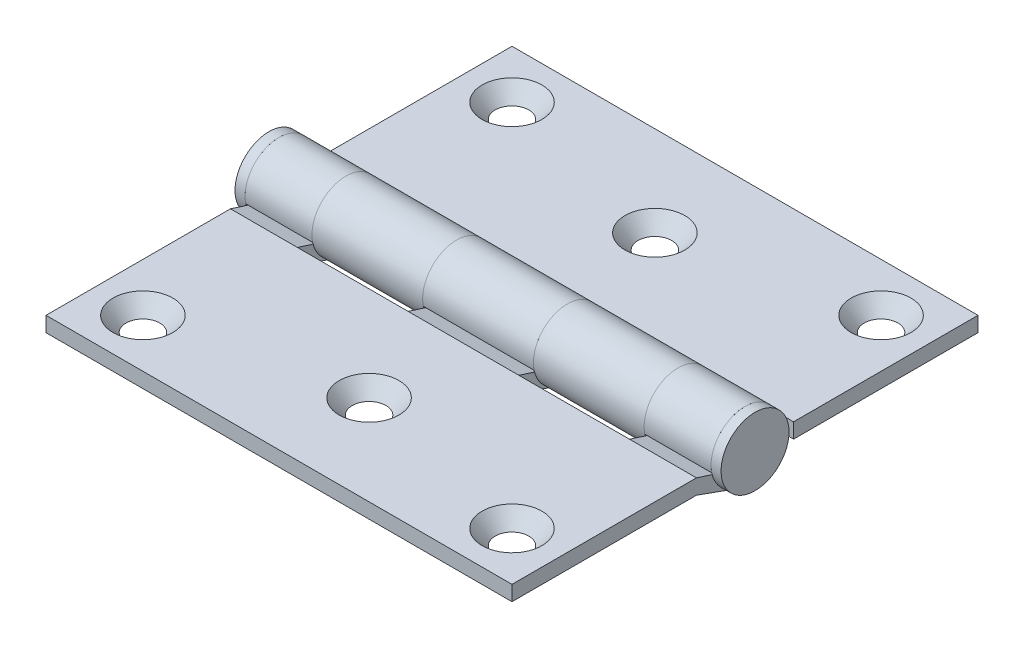
SolidWorks part; units mm, degrees
ref_plane "Front" through (0, 0, 0) normal (0, 0, 1) x (1, 0, 0)
ref_plane "Top" through (0, 0, 0) normal (0, 1, 0) x (1, 0, 0)
ref_plane "Right" through (0, 0, 0) normal (1, 0, 0) x (0, 0, -1)
sketch "Sketch1" plane through (0, 0, 0) normal (1, 0, 0) x (0, 0, -1)
  line L0 (-7.9375, -3.048) -> (-1.8819, -5.2279)
  line L1 (-38.1, -0.5842) -> (-7.9375, -0.5842)
  line L2 (-7.9375, -0.5842) -> (-0.9076, -2.8348)
  line L3 (-38.1, -3.048) -> (-7.9375, -3.048)
  line L4 (-38.1, -0.5842) -> (-38.1, -3.048)
  line L5 (-5.443, -1.1161) -> (-1.976, -2.2261)
  arc A0 (-0.9076, -2.8348) -> (-1.976, -2.2261) centre (0, 0) ccw
  arc A1 (-1.8819, -5.2279) -> (-5.443, -1.1161) centre (0, 0) ccw
  circle A2 centre (0, 0) radius 5.5562 construction
  circle A3 centre (0, 0) radius 2.9766 construction
  dimension "Pin Dia." = 5.9531
  dimension "Kn Dia" = 11.1125
  dimension "Th" = 2.4638
  dimension "D3" = 0.254
  dimension "Open Width / 2" = 38.1
  dimension "Leaf End" = 30.1625
  dimension "Leaf Top" = 0.5842
extrude "Left Leaf" add sketch "Sketch1" along normal mid plane 76.2
sketch "Sketch2" plane through (0, 0, 0) normal (0, 1, 0) x (1, 0, 0)
  line L0 (27.1577, -7.9375) -> (27.1577, 5.5563)
  line L2 (0, 5.5562) -> (0, -38.1) construction
  line L3 (38.1, 5.5563) -> (-38.1, 5.5563) construction
  line L4 (27.1577, 5.5563) -> (9.0526, 5.5563)
  line L5 (9.0526, 5.5563) -> (9.0526, -7.9375)
  line L7 (38.1, -38.1) -> (-38.1, -38.1) construction
  line L8 (-27.1577, -7.9375) -> (-27.1577, 5.5562)
  line L9 (9.0526, -7.9375) -> (27.1577, -7.9375)
  line L10 (-9.0526, -7.9375) -> (-27.1577, -7.9375)
  line L11 (-9.0526, 5.5563) -> (-9.0526, -7.9375)
  line L12 (-27.1577, 5.5562) -> (-9.0526, 5.5563)
  line L14 (-9.0526, 5.5563) -> (9.0526, 5.5563) construction
  dimension "Knuckle Lg" = 18.1051
extrude "Cut-Extrude1" cut sketch "Sketch2" against normal through all and the other way through all
sketch "Sketch3" plane through (27.1577, 0, 0) normal (1, 0, 0) x (0, 0, -1)
  line L0 (0, 5.5563) -> (0, -3.048) construction
  line L1 (-38.1, -3.048) -> (-7.9375, -3.048) construction
  line L2 (7.9375, -3.048) -> (1.8819, -5.2279)
  line L3 (7.9375, -0.5842) -> (0.9076, -2.8348)
  line L4 (1.976, -2.2261) -> (5.443, -1.1161)
  line L6 (7.9375, -3.048) -> (38.1, -3.048)
  line L7 (38.1, -3.048) -> (38.1, -0.5842)
  line L9 (-38.1, -0.5842) -> (-38.1, -3.048) construction
  line L10 (38.1, -0.5842) -> (7.9375, -0.5842)
  arc A0 (-1.8819, -5.2279) -> (-5.443, -1.1161) centre (0, 0) ccw construction
  circle A5 centre (0, 0) radius 5.5563 construction
  arc A6 (1.8819, -5.2279) -> (5.443, -1.1161) centre (0, 0) cw
  arc A7 (-0.9076, -2.8348) -> (-1.976, -2.2261) centre (0, 0) ccw construction
  arc A8 (1.976, -2.2261) -> (0.9076, -2.8348) centre (0, 0) ccw
extrude "Right Leaf" add sketch "Sketch3" against normal up to surface (18.1051 mm away) separate body up to face at (9.0526, -0.5185, 2.5509)
mirror "Mirror1" about plane through (0, 0, 0) normal (1, 0, 0) of bodies 110
sketch "Sketch4" plane through (0, 0, 0) normal (-1, 0, 0) x (0, 0, 1)
  line L0 (-7.9375, -0.5842) -> (-7.9375, -3.048)
  line L1 (-38.1, -0.5842) -> (-7.9375, -0.5842)
  line L2 (0, 5.5563) -> (0, -3.048) construction
  line L6 (-7.9375, -3.048) -> (-38.1, -3.048)
  line L8 (-38.1, -3.048) -> (-38.1, -0.5842)
extrude "Extrude3" add sketch "Sketch4" along normal up to surface and the other way up to surface
combine bodies "Combine1" operation type add bodies to combine 125 110 111
sketch "Sketch6" plane through (0, 0, 0) normal (0, 1, 0) x (1, 0, 0)
  line L0 (24.5662, 0) -> (-23.3403, 0) construction
  line L1 (38.1, -5.5563) -> (38.1, 5.5563) construction
  line L2 (-38.1, 0) -> (38.1, 0)
  line L3 (-38.1, 0) -> (-38.1, -2.9766)
  line L4 (-38.1, -2.9766) -> (38.1, -2.9766)
  line L5 (38.1, 0) -> (38.1, -2.9766)
  line L6 (-38.1, -2.9766) -> (-38.1, 2.9766) construction
  dimension "D1" = 5.9531
revolve "Pin" add sketch "Sketch6" angle 360 about L0
sketch "Sketch7" plane through (0, 0, 0) normal (0, 1, 0) x (1, 0, 0)
  line L0 (24.5662, 0) -> (-23.3403, 0) construction
  line L1 (0, 38.1) -> (0, -38.1) construction
  line L2 (24.5662, 0) -> (-23.3403, 0) construction
  line L3 (-39.7425, 0) -> (-39.7425, -5.5563)
  line L4 (-39.7425, 0) -> (-38.1, 0)
  line L5 (-38.1, 0) -> (-38.1, -5.5563)
  line L6 (-38.1, 38.1) -> (38.1, 38.1) construction
  line L7 (-39.7425, -5.5563) -> (-38.1, -5.5563)
  line L8 (39.7425, 0) -> (39.7425, -5.5562)
  line L9 (38.1, 0) -> (38.1, -5.5562)
  line L10 (39.7425, 0) -> (38.1, 0)
  line L11 (39.7425, -5.5562) -> (38.1, -5.5562)
  dimension "D1" = 1.6425
revolve "Spun Pin" add sketch "Sketch7" angle 360 about L0
sketch "Sketch8" plane through (0, -0.5842, 0) normal (0, 1, 0) x (-1, 0, 0)
  line L3 (38.1, 0) -> (-38.1, 0) construction
  line L4 (0, -38.1) -> (0, 38.1) construction
  line L5 (38.1, -38.1) -> (-38.1, -38.1) construction
  line L6 (0, 38.1) -> (0, 7.9375) construction
  line L7 (-38.1, 38.1) -> (38.1, 38.1) construction
  point P3 (30.1752, -30.1752)
  point P4 (-30.1752, -30.1752)
  point P8 (-30.1752, 30.1752)
  point P9 (30.1752, 30.1752)
  point P26 (0, -23.368)
  point P27 (0, 23.368)
  dimension "Hole Dist" = 30.1752
  dimension "Hole Dist2" = 7.9248
  dimension "Hole Dist3" = 14.732
hole_wizard "CSK for #10 Flat Head Machine Screw1" positions "3DSketch1" profile "Sketch9" countersink size "#10" standard "Ansi Inch" end condition through all
sketch3d "3DSketch1"
  point P30 (-30.1752, -0.5842, 30.1752)
  point P33 (-30.1752, -0.5842, -30.1752)
  point P36 (30.1752, -0.5842, -30.1752)
  point P39 (30.1752, -0.5842, 30.1752)
  point P56 (0, -0.5842, -23.368)
  point P59 (0, -0.5842, 23.368)
sketch "Sketch9" plane through (-30.1752, -0.5842, 30.1752) normal (1, 0, 0) x (0, 0, 1)
  line L0 (0, 0) -> (0, 4.972)
  line L1 (0, 4.972) -> (2.5527, 4.972)
  line L2 (2.5527, 4.972) -> (2.5527, 2.6882)
  line L3 (2.5527, 2.6882) -> (4.8895, 0)
  line L5 (4.8895, 0) -> (0, 0)
  line L6 (-2.5527, 2.6882) -> (-4.8895, 0) construction
  line L11 (0, -6.35) -> (0, 107.95) construction
  dimension "Thru Hole Dia." = 5.1054
  dimension "Thru Hole Depth" = 4.9721
  dimension "Near C'Sink Dia." = 9.779
  dimension "Near C'Sink Angle" = 82
equation "\"D1@Sketch7\"=\"Th@Sketch1\"/1.5"
equation "\"D1@Sketch6\" = \"Pin Dia.@Sketch1\""
